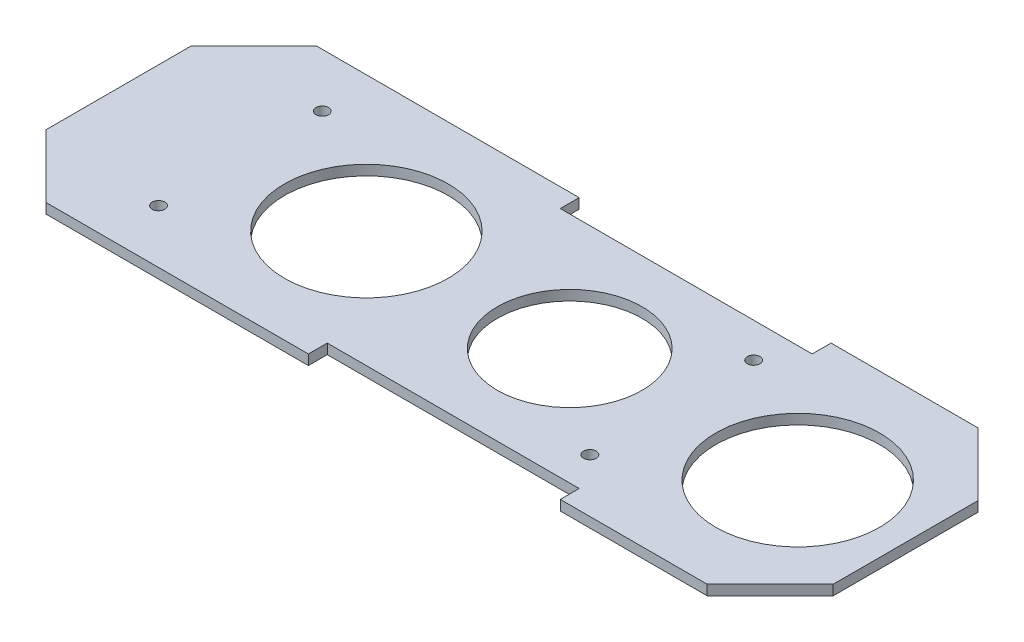
SolidWorks part; units mm, degrees
ref_plane "Front Plane" through (0, 0, 0) normal (0, 0, 1) x (1, 0, 0)
ref_plane "Top Plane" through (0, 0, 0) normal (0, 1, 0) x (1, 0, 0)
ref_plane "Right Plane" through (0, 0, 0) normal (1, 0, 0) x (0, 0, -1)
sketch "Sketch2" plane through (0, 0, 0) normal (0, 1, 0) x (1, 0, 0)
  line L0 (0, 0) -> (162.4584, 0) construction
  line L1 (0, 21.5) -> (51.6667, 21.5)
  line L2 (0, 21.5) -> (0, -21.5)
  line L3 (0, -21.5) -> (51.6667, -21.5)
  line L4 (125, 21.5) -> (125, -21.5)
  line L5 (51.6667, -18.5) -> (91.6667, -18.5)
  line L6 (51.6667, 21.5) -> (91.6667, 21.5) construction
  line L7 (51.6667, 21.5) -> (51.6667, 18.5)
  line L8 (51.6667, 18.5) -> (91.6667, 18.5)
  line L9 (91.6667, 21.5) -> (91.6667, 18.5)
  line L10 (91.6667, -21.5) -> (91.6667, -18.5)
  line L11 (51.6667, -21.5) -> (91.6667, -21.5) construction
  line L12 (51.6667, -21.5) -> (51.6667, -18.5)
  line L13 (51.6667, 21.5) -> (91.6667, 21.5) construction
  line L14 (91.6667, 21.5) -> (125, 21.5)
  line L15 (51.6667, -21.5) -> (91.6667, -21.5) construction
  line L16 (91.6667, -21.5) -> (125, -21.5)
  circle A0 centre (19.37, 13) radius 1
  circle A1 centre (87.87, 13) radius 1
  circle A2 centre (87.87, -13) radius 1
  circle A3 centre (19.37, -13) radius 1
  circle A4 centre (39.37, 0) radius 13
  circle A5 centre (107.87, 0) radius 13
  circle A6 centre (71.6667, 0) radius 11.5
  point P4 (0, 0)
  point P30 (39.8118, 0)
  point P31 (107.6988, 0)
  point P32 (0, 0)
  point P33 (71.6667, -18.5)
  dimension "D6" = 37.13
  dimension "D8" = 2
  dimension "D9" = 2
  dimension "D11" = 26
  dimension "D12" = 26
  dimension "D15" = 23
  dimension "D1" = 125
  dimension "D2" = 43
  dimension "D3" = 3
  dimension "D4" = 40
  dimension "D5" = 33.3333
  dimension "D7" = 68.5
  dimension "D10" = 13
  dimension "D13" = 20
  dimension "D14" = 20
extrude "Boss-Extrude1" add sketch "Sketch2" along normal blind 1.6 contours L2 L0 A4 A6 A5 L4 L1 L9 L8 L7 A0 A1 | L0 L2 L3 L12 L5 L10 L4 A5 A6 A4 A2 A3
chamfer "Chamfer1" distance 10 angle 45 4 edges at (0, 0.8, 21.5) (0, 0.8, -21.5) (125, 0.8, -21.5) (125, 0.8, 21.5)
